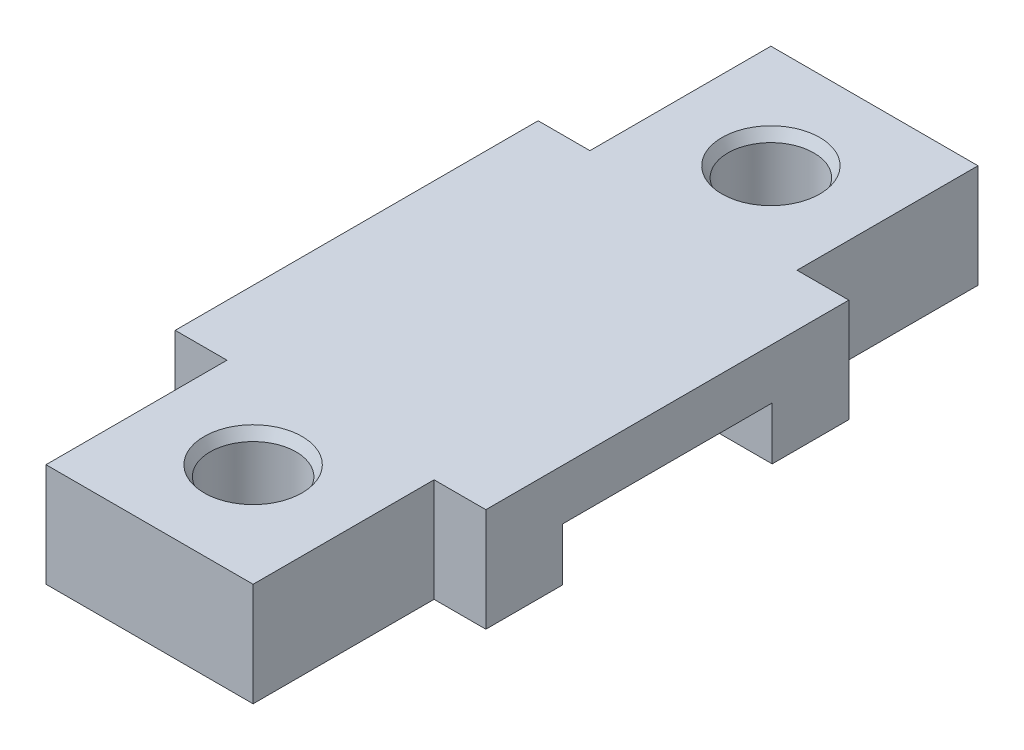
SolidWorks part; units mm, degrees
ref_plane "Спереди" through (0, 0, 0) normal (0, 0, 1) x (1, 0, 0)
ref_plane "Сверху" through (0, 0, 0) normal (0, 1, 0) x (1, 0, 0)
ref_plane "Справа" through (0, 0, 0) normal (1, 0, 0) x (0, 0, -1)
sketch "Sketch1" plane through (0, 0, 0) normal (0, 1, 0) x (1, 0, 0)
  line L1 (10, -35) -> (-10, -35)
  line L2 (10, -35) -> (10, 35)
  line L3 (10, 35) -> (-10, 35)
  line L4 (-10, -35) -> (-10, 35)
  line L5 (10, -35) -> (-10, 35) construction
  line L6 (10, 35) -> (-10, -35) construction
  point P0 (0, 0)
  dimension "D1" = 20
  dimension "D2" = 70
extrude "Boss-Extrude1" add sketch "Sketch1" along normal blind 10
sketch "Sketch2" plane through (10, 0, 0) normal (1, 0, 0) x (0, 0, -1)
  line L0 (0, 0) -> (0, 10) construction
  line L1 (-35, 0) -> (35, 0) construction
  line L2 (-35, 10) -> (35, 10) construction
  line L4 (10.125, 5.1) -> (-10.125, 5.1)
  line L5 (10.125, 5.1) -> (10.125, 0)
  line L6 (10.125, 0) -> (-10.125, 0)
  line L7 (-10.125, 5.1) -> (-10.125, 0)
  line L8 (10.125, 5.1) -> (-10.125, 0) construction
  line L9 (10.125, 0) -> (-10.125, 5.1) construction
  point P6 (0, 2.55)
  dimension "D1" = 20.25
  dimension "D2" = 5.1
extrude "Cut-Extrude1" cut sketch "Sketch2" against normal through all and the other way through all
sketch "Sketch3" plane through (0, 0, 0) normal (0, -1, 0) x (1, 0, 0)
  line L0 (0, 35) -> (0, -35) construction
  line L1 (-10, 35) -> (10, 35) construction
  line L2 (10, -35) -> (-10, -35) construction
  circle A0 centre (0, 25) radius 4.15
  circle A1 centre (0, -25) radius 4.15
  dimension "D1" = 8.3
  dimension "D2" = 25
  dimension "D3" = 50
extrude "Cut-Extrude2" cut sketch "Sketch3" against normal through all
sketch "Sketch4" plane through (10, 0, 0) normal (1, 0, 0) x (0, 0, -1)
  line L0 (-10.125, 0) -> (-17.525, 0)
  line L1 (-35, 0) -> (-10.125, 0) construction
  line L2 (-17.525, 0) -> (-17.525, 10)
  line L3 (-35, 10) -> (35, 10) construction
  line L4 (-17.525, 10) -> (17.525, 10)
  line L5 (17.525, 10) -> (17.525, 0)
  line L6 (10.125, 0) -> (35, 0) construction
  line L7 (17.525, 0) -> (10.125, 0)
  line L8 (10.125, 0) -> (10.125, 5.1)
  line L9 (10.125, 5.1) -> (-10.125, 5.1)
  line L10 (-10.125, 5.1) -> (-10.125, 0)
  dimension "D1" = 7.4
extrude "Boss-Extrude2" add sketch "Sketch4" along normal blind 5 and the other way blind 25
chamfer "Chamfer1" distance 1 angle 30 2 edges at (0, 10, -29.15) (0, 10, 20.85)
